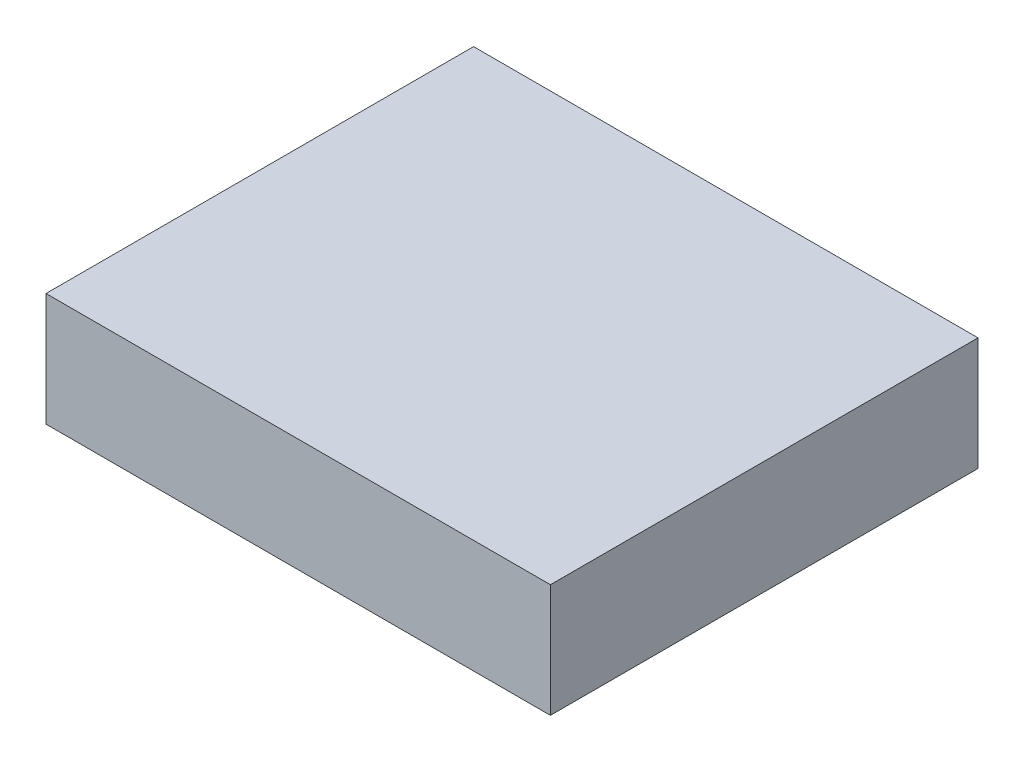
SolidWorks part; units mm, degrees
ref_plane "Front Plane" through (0, 0, 0) normal (0, 0, 1) x (1, 0, 0)
ref_plane "Top Plane" through (0, 0, 0) normal (0, 1, 0) x (1, 0, 0)
ref_plane "Right Plane" through (0, 0, 0) normal (1, 0, 0) x (0, 0, -1)
sketch "Sketch1" plane through (0, 0, 0) normal (0, 1, 0) x (1, 0, 0)
  line L1 (-390, -330.6068) -> (390, -330.6068)
  line L2 (-390, -330.6068) -> (-390, 330.6068)
  line L3 (-390, 330.6068) -> (390, 330.6068)
  line L4 (390, -330.6068) -> (390, 330.6068)
  line L5 (-390, -330.6068) -> (390, 330.6068) construction
  line L6 (-390, 330.6068) -> (390, -330.6068) construction
  point P0 (0, 0)
  dimension "D1" = 661.2136
  dimension "D2" = 780
extrude "Boss-Extrude1" add sketch "Sketch1" along normal blind 175
